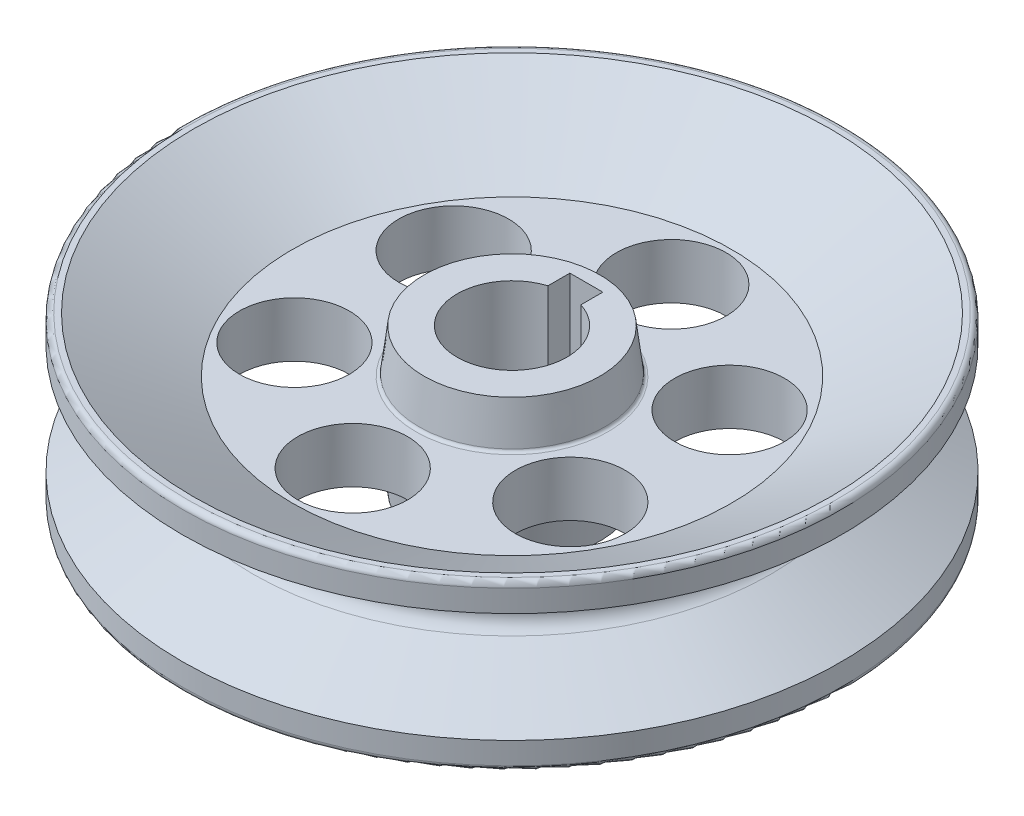
SolidWorks part; units mm, degrees
ref_plane "Front Plane" through (0, 0, 0) normal (0, 0, 1) x (1, 0, 0)
ref_plane "Top Plane" through (0, 0, 0) normal (0, 1, 0) x (1, 0, 0)
ref_plane "Right Plane" through (0, 0, 0) normal (1, 0, 0) x (0, 0, -1)
sketch "Sketch1" plane through (0, 0, 0) normal (0, 1, 0) x (1, 0, 0)
  circle A0 centre (0, 0) radius 1524
extrude "Boss-Extrude1" add sketch "Sketch1" along normal mid plane 762
sketch "Sketch2" plane through (0, 0, 0) normal (1, 0, 0) x (0, 0, -1)
  line L0 (1524, -254) -> (1524, 254)
  line L2 (1524, -381) -> (1524, 381) construction
  line L3 (1524, 254) -> (1198.3591, 65.9911)
  line L5 (1676.4, 0) -> (-1676.4, 0) construction
  line L7 (1524, -254) -> (1198.3591, -65.9911)
  arc A0 (1198.3591, 65.9911) -> (1198.3591, -65.9911) centre (1236.4591, 0) ccw
  dimension "D1" = 254
revolve "Cut-Revolve1" cut sketch "Sketch2" angle 360 about axis through (0, 381, 0) along (0, -1, 0)
sketch "Sketch3" plane through (0, 381, 0) normal (0, 1, 0) x (1, 0, 0)
  line L0 (-76.2, 242.3006) -> (-76.2, 343.9006)
  line L1 (-76.2, 343.9006) -> (76.2, 343.9006)
  line L2 (76.2, 343.9006) -> (76.2, 242.3006)
  arc A0 (-76.2, 242.3006) -> (76.2, 242.3006) centre (0, 0) ccw
  dimension "D1" = 508
  dimension "D2" = 152.4
  dimension "D3" = 101.6
extrude "Cut-Extrude1" cut sketch "Sketch3" against normal through all
sketch "Sketch4" plane through (0, 381, 0) normal (0, 1, 0) x (1, 0, 0)
  circle A0 centre (0, 0) radius 736.6 construction
  circle A1 centre (0, 736.6) radius 254
  dimension "D1" = 736.6
  dimension "D2" = 508
extrude "Cut-Extrude2" cut sketch "Sketch4" against normal through all
pattern_circular "CirPattern1" count 6 every 60 about axis through (0, 0, 0) along (0, 1, 0) of "Cut-Extrude2"
sketch "Sketch7" plane through (0, 0, 0) normal (1, 0, 0) x (0, 0, -1)
  line L1 (406.4, 330.2) -> (430.1375, 139.684)
  line L2 (-1524, -381) -> (1524, -381) construction
  line L3 (0, -330.2) -> (0, -381)
  line L4 (1473.2, -381) -> (0, -381)
  line L5 (406.4, -330.2) -> (430.1375, -139.684)
  line L6 (1524, -381) -> (1524, -254) construction
  line L7 (0, -330.2) -> (406.4, -330.2)
  line L8 (1473.2, -381) -> (1016, -127)
  line L9 (1016, 127) -> (444.5, 127)
  line L10 (1473.2, 381) -> (1016, 127)
  line L11 (1016, -127) -> (444.5, -127)
  line L12 (1473.2, 381) -> (0, 381)
  line L13 (0, 330.2) -> (0, 381)
  line L14 (0, 330.2) -> (406.4, 330.2)
  arc A1 (444.5, -127) -> (430.1375, -139.684) centre (444.5, -141.4735) ccw
  arc A2 (444.5, 127) -> (430.1375, 139.684) centre (444.5, 141.4735) cw
  point P7 (1473.2, -381)
  dimension "D1" = 50.8
  dimension "D2" = 50.8
revolve "Cut-Revolve3" cut sketch "Sketch7" angle 360 about axis through (0, 254, 0) along (0, 1, 0)
fillet "Fillet3" radius 25.4 2 edges at (0, 381, 1524) (0, -381, 1524)
